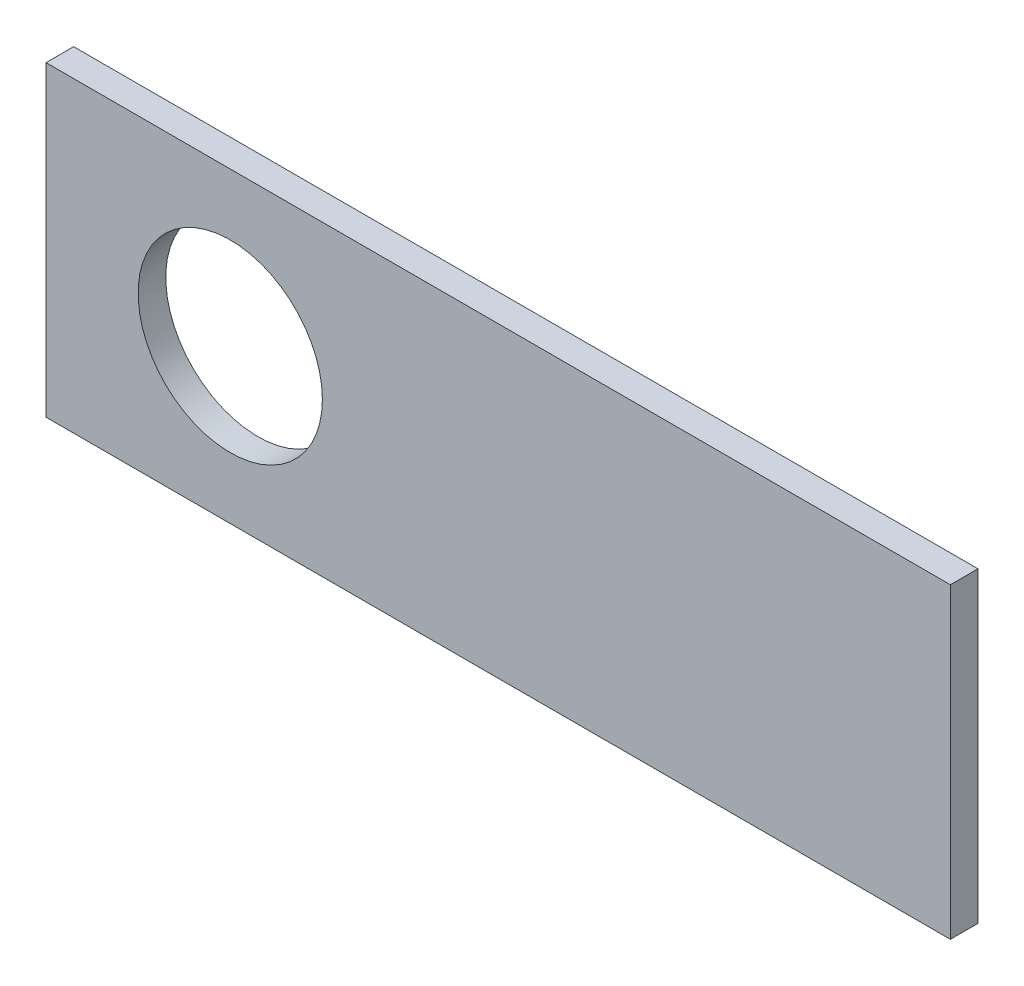
SolidWorks part; units mm, degrees
ref_plane "Спереди" through (0, 0, 0) normal (0, 0, 1) x (1, 0, 0)
ref_plane "Сверху" through (0, 0, 0) normal (0, 1, 0) x (1, 0, 0)
ref_plane "Справа" through (0, 0, 0) normal (1, 0, 0) x (0, 0, -1)
sketch "Эскиз1" plane through (0, 0, 0) normal (0, 0, 1) x (1, 0, 0)
  line L1 (294.5, -100) -> (-294.5, -100)
  line L2 (294.5, -100) -> (294.5, 100)
  line L3 (294.5, 100) -> (-294.5, 100)
  line L4 (-294.5, -100) -> (-294.5, 100)
  line L5 (294.5, -100) -> (-294.5, 100) construction
  line L6 (294.5, 100) -> (-294.5, -100) construction
  point P0 (0, 0)
  dimension "D1" = 589
  dimension "D2" = 200
extrude "Бобышка-Вытянуть1" add sketch "Эскиз1" along normal blind 18
sketch "Эскиз2" plane through (0, 0, 18) normal (0, 0, 1) x (1, 0, 0)
  line L0 (-294.5, 100) -> (-294.5, -100) construction
  line L1 (-294.5, -100) -> (294.5, -100) construction
  circle A0 centre (-174.5, 0) radius 60
  dimension "D1" = 120
  dimension "D2" = 120
  dimension "D3" = 100
extrude "Вырез-Вытянуть1" cut sketch "Эскиз2" against normal through all
